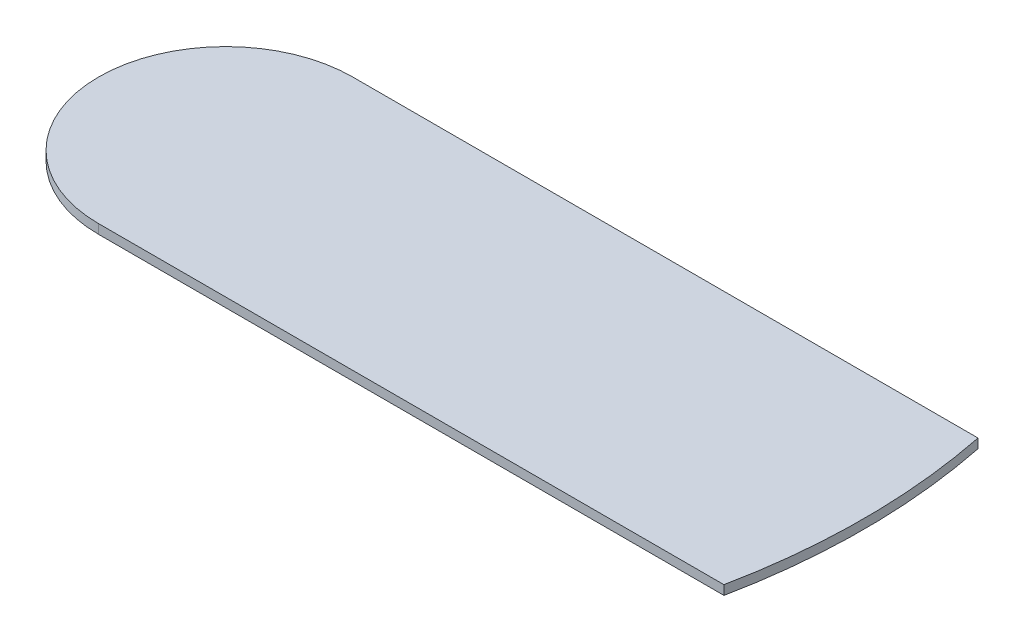
SolidWorks part; units mm, degrees
material "6061-T6 (SS)"
ref_plane "Front" through (0, 0, 0) normal (0, 0, 1) x (1, 0, 0)
ref_plane "Top" through (0, 0, 0) normal (0, 1, 0) x (1, 0, 0)
ref_plane "Right" through (0, 0, 0) normal (1, 0, 0) x (0, 0, -1)
sketch "Sketch1" plane through (0, 0, 0) normal (0, 1, 0) x (1, 0, 0)
  line L3 (0, -26.575) -> (130.8282, -26.575)
  line L7 (0, 26.575) -> (130.8282, 26.575)
  arc A0 (133.5, 0) -> (130.8282, -26.575) centre (0, 0) cw
  arc A1 (0, 26.575) -> (0, -26.575) centre (0, 0) ccw
  arc A2 (133.5, 0) -> (130.8282, 26.575) centre (0, 0) ccw
extrude "Boss-Extrude1" add sketch "Sketch1" along normal blind 1.95 contours L3 A0 A2 L7 A1
